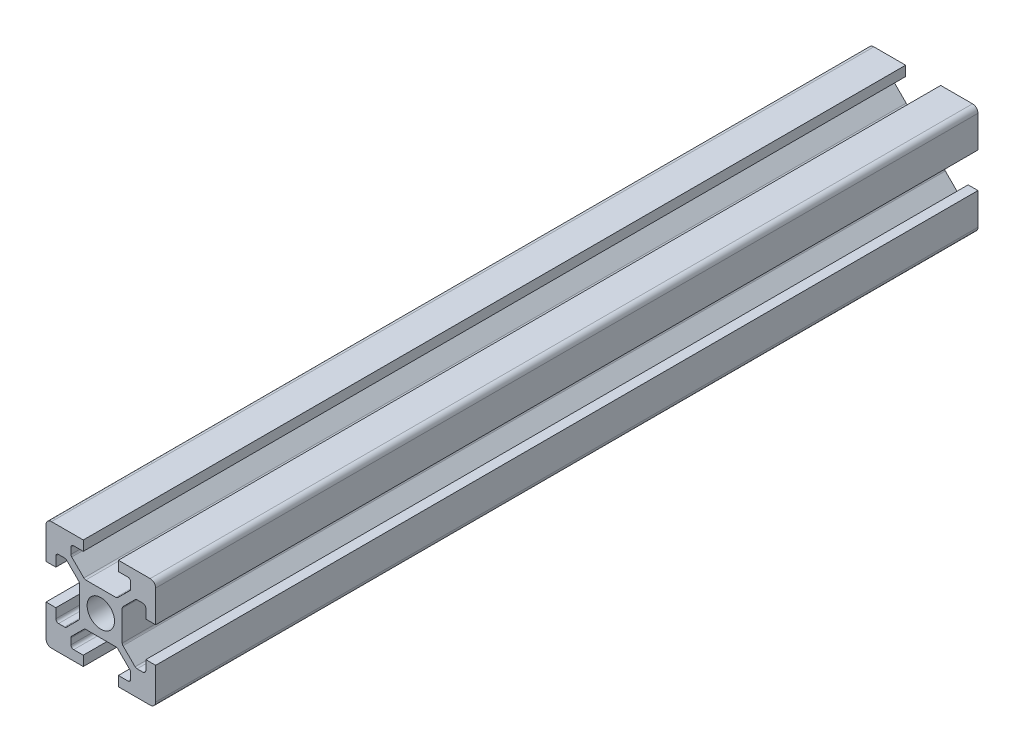
SolidWorks part; units mm, degrees
material "1060 Alloy"
ref_plane "Front Plane" through (0, 0, 0) normal (0, 0, 1) x (1, 0, 0)
ref_plane "Top Plane" through (0, 0, 0) normal (0, 1, 0) x (1, 0, 0)
ref_plane "Right Plane" through (0, 0, 0) normal (1, 0, 0) x (0, 0, -1)
sketch "Sketch1" plane through (0, 0, 0) normal (0, 0, 1) x (1, 0, 0)
  line L0 (20, 0) -> (-8.059, 28.059) construction
  line L1 (0, 0) -> (6.8, 0)
  line L2 (0, 0) -> (0, 6.8)
  line L3 (0, 20) -> (6.8, 20)
  line L4 (20, 0) -> (20, 6.8)
  line L5 (6.8, 20) -> (6.8, 18.2)
  line L6 (20, 20) -> (8.2322, 8.2322) construction
  line L7 (12.95, 6.1) -> (7.05, 6.1)
  line L8 (13.9, 7.05) -> (13.9, 12.95)
  line L9 (12.95, 13.9) -> (7.05, 13.9)
  line L10 (6.1, 7.05) -> (6.1, 12.95)
  line L11 (13.9, 6.1) -> (6.1, 13.9) construction
  line L12 (13.9, 13.9) -> (6.1, 6.1) construction
  line L13 (4.55, 16.4) -> (7.05, 13.9)
  line L14 (13.2, 18.2) -> (13.2, 20)
  line L15 (1.8, 6.8) -> (0, 6.8)
  line L16 (0, 13.2) -> (0, 20)
  line L17 (0, 13.2) -> (1.8, 13.2)
  line L18 (10, 10) -> (10, 13.9) construction
  line L19 (16.4, 4.55) -> (13.9, 7.05)
  line L20 (4.55, 16.4) -> (4.55, 18.2)
  line L21 (4.55, 18.2) -> (6.8, 18.2)
  line L22 (13.2, 18.2) -> (15.45, 18.2)
  line L23 (15.45, 18.2) -> (15.45, 16.4)
  line L24 (15.45, 16.4) -> (12.95, 13.9)
  line L25 (16.4, 4.55) -> (18.2, 4.55)
  line L26 (18.2, 4.55) -> (18.2, 6.8)
  line L27 (20, 6.8) -> (18.2, 6.8)
  line L28 (18.2, 13.2) -> (20, 13.2)
  line L29 (18.2, 13.2) -> (18.2, 15.45)
  line L30 (18.2, 15.45) -> (16.4, 15.45)
  line L31 (16.4, 15.45) -> (13.9, 12.95)
  line L32 (1.8, 4.55) -> (3.6, 4.55)
  line L33 (3.6, 15.45) -> (6.1, 12.95)
  line L34 (3.6, 15.45) -> (1.8, 15.45)
  line L35 (1.8, 15.45) -> (1.8, 13.2)
  line L36 (0, 13.2) -> (1.8, 13.2)
  line L37 (1.8, 6.8) -> (0, 6.8)
  line L38 (3.6, 4.55) -> (6.1, 7.05)
  line L39 (1.8, 6.8) -> (1.8, 4.55)
  line L40 (15.45, 3.6) -> (12.95, 6.1)
  line L41 (4.55, 3.6) -> (7.05, 6.1)
  line L42 (4.55, 1.8) -> (4.55, 3.6)
  line L43 (6.8, 1.8) -> (4.55, 1.8)
  line L44 (6.8, 1.8) -> (6.8, 0)
  line L45 (15.45, 3.6) -> (15.45, 1.8)
  line L46 (15.45, 1.8) -> (13.2, 1.8)
  line L47 (13.2, 0) -> (13.2, 1.8)
  line L48 (13.2, 20) -> (20, 20)
  line L49 (20, 13.2) -> (20, 20)
  line L50 (13.2, 0) -> (20, 0)
  line L51 (6.1, 6.1) -> (-5.5045, -5.5045) construction
  circle A0 centre (10, 10) radius 2.5
  point P25 (10, 16.4)
  point P39 (13.2, 19.1)
  point P46 (0.9, 6.8)
  dimension "D3" = 5
  dimension "D2" = 20
  dimension "D4" = 7.8
  dimension "D5" = 7.8
  dimension "D6" = 6.8
  dimension "D7" = 6.8
  dimension "D8" = 1.8
  dimension "D9" = 10.9
  dimension "D10" = 1.8
  dimension "D11" = 10.9
  dimension "D12" = 20
extrude "Boss-Extrude1" add sketch "Sketch1" along normal blind 150 contours L47 L50 L4 L27 L26 L25 L19 L8 L31 L30 L29 L28 L49 L48 L14 L22 L23 L24 L9 L13 L20 L21 L5 L3 L16 L17 L35 L34 L33 L10 L38 L32 L39 L15 L2 L1 L44 L43 L42 L41 L7 L40 L45 L46 A0
fillet "Fillet1" radius 1 4 edges at (20, 20, 75) (20, 0, 75) (0, 0, 75) (0, 20, 75)
fillet "Fillet2" radius 0.5 6 edges at (4.55, 18.2, 75) (4.55, 16.4, 75) (7.05, 13.9, 75) (15.45, 18.2, 75) (15.45, 16.4, 75) (12.95, 13.9, 75)
fillet "Fillet3" radius 0.5 6 edges at (18.2, 15.45, 75) (16.4, 15.45, 75) (13.9, 12.95, 75) (18.2, 4.55, 75) (13.9, 7.05, 75) (16.4, 4.55, 75)
fillet "Fillet4" radius 0.5 6 edges at (1.8, 15.45, 75) (3.6, 15.45, 75) (6.1, 12.95, 75) (3.6, 4.55, 75) (1.8, 4.55, 75) (6.1, 7.05, 75)
fillet "Fillet5" radius 0.5 6 edges at (7.05, 6.1, 75) (4.55, 3.6, 75) (4.55, 1.8, 75) (15.45, 1.8, 75) (15.45, 3.6, 75) (12.95, 6.1, 75)
